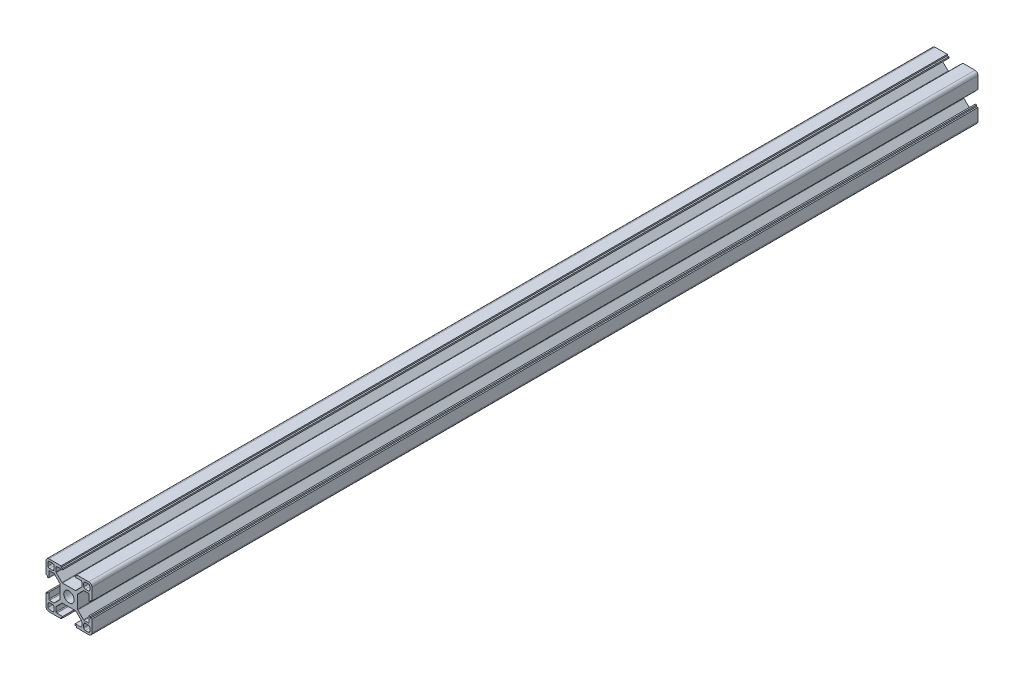
SolidWorks part; units mm, degrees
ref_plane "前视基准面" through (0, 0, 0) normal (0, 0, 1) x (1, 0, 0)
ref_plane "上视基准面" through (0, 0, 0) normal (0, 1, 0) x (1, 0, 0)
ref_plane "右视基准面" through (0, 0, 0) normal (1, 0, 0) x (0, 0, -1)
sketch "草图1" plane through (0, 0, 0) normal (0, 0, 1) x (1, 0, 0)
  line L0 (0, 0) -> (0, 65.3905) construction
  line L1 (0, 0) -> (64.2648, 0) construction
  line L2 (0, 0) -> (79.9729, 79.9729) construction
  line L3 (5.7, 0) -> (5.7, 4.4272)
  line L4 (5.7, 4.4272) -> (9.6728, 8.4)
  line L5 (9.6728, 8.4) -> (13.2, 8.4)
  line L6 (13.2, 8.4) -> (13.2, 4.1)
  line L7 (13.2, 4.1) -> (14.1, 4.1)
  line L8 (14.1, 4.1) -> (14.1, 5.1)
  line L9 (14.1, 5.1) -> (15, 5.1)
  line L10 (15, 5.1) -> (15, 15)
  line L11 (5.1, 15) -> (15, 15)
  line L12 (5.1, 14.1) -> (5.1, 15)
  line L13 (4.1, 14.1) -> (5.1, 14.1)
  line L14 (4.1, 13.2) -> (4.1, 14.1)
  line L15 (8.4, 13.2) -> (4.1, 13.2)
  line L16 (8.4, 9.6728) -> (8.4, 13.2)
  line L17 (4.4272, 5.7) -> (8.4, 9.6728)
  line L18 (0, 5.7) -> (4.4272, 5.7)
  line L20 (9.7, 9.7) -> (13.7, 9.7)
  line L21 (9.7, 9.7) -> (9.7, 13.7)
  line L22 (9.7, 13.7) -> (13.7, 13.7)
  line L23 (13.7, 9.7) -> (13.7, 13.7)
  line L24 (9.7, 9.7) -> (13.7, 13.7) construction
  line L25 (9.7, 13.7) -> (13.7, 9.7) construction
  line L26 (0, 5.7) -> (0, 0)
  line L27 (0, 0) -> (5.7, 0)
  point P9 (11.7, 11.7)
  dimension "D1" = 45
  dimension "D2" = 5.7
  dimension "D3" = 1.8
  dimension "D4" = 0.9
  dimension "D5" = 8.2
  dimension "D6" = 10.2
  dimension "D7" = 1.8
  dimension "D8" = 15
  dimension "D9" = 16.8
  dimension "D10" = 4
  dimension "D11" = 1.3
extrude "凸台-拉伸1" add sketch "草图1" along normal blind 580 contours L3 L4 L5 L6 L7 L8 L9 L10 L11 L12 L13 L14 L15 L16 L17 L18 L26 L27
fillet "圆角1" radius 1 4 edges at (9.7, 9.7, 290) (13.7, 9.7, 290) (9.7, 13.7, 290) (13.7, 13.7, 290)
fillet "圆角2" radius 2 1 edges at (15, 15, 290)
fillet "圆角3" radius 0.5 6 edges at (5.7, 4.4272, 290) (4.4272, 5.7, 290) (8.4, 13.2, 290) (8.4, 9.6728, 290) (9.6728, 8.4, 290) (13.2, 8.4, 290)
pattern_circular "阵列(圆周)1" count 4 over 360 about axis through (0, 0, 0) along (0, 0, 1) of "圆角2", "圆角3", "凸台-拉伸1", "圆角1"
sketch "草图2" plane through (0, 0, 580) normal (0, 0, 1) x (1, 0, 0)
  circle A0 centre (0, 0) radius 3.4
  dimension "D1" = 6.8
extrude "切除-拉伸1" cut sketch "草图2" against normal through all
sketch "草图3" plane through (0, 0, 0) normal (0, 1, 0) x (1, 0, 0)
  line L0 (0, 51.9441) -> (0, -638.1502) construction
  line L1 (13, 0) -> (5.1, 0) construction
  circle A0 centre (0, -30) radius 2.6
  circle A1 centre (0, -90) radius 2.6
  dimension "D1" = 60
  dimension "D3" = 5.2
  dimension "D2" = 30
extrude "切除-拉伸2" cut sketch "草图3" against normal mid plane 20
